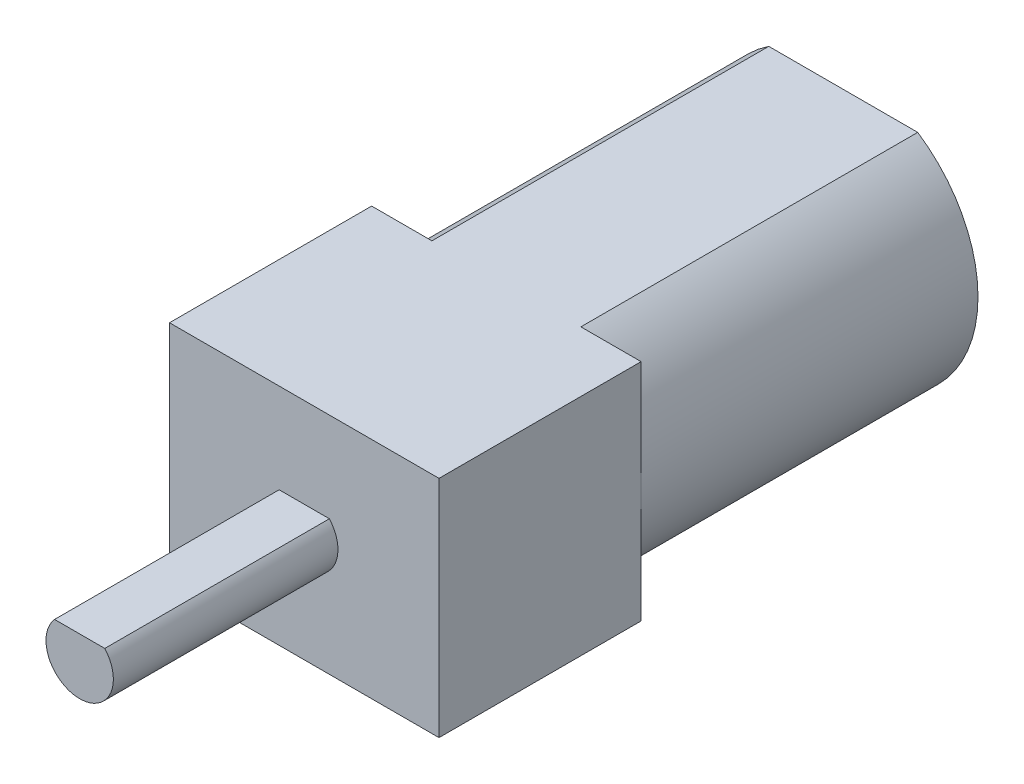
SolidWorks part; units mm, degrees
ref_plane "Front Plane" through (0, 0, 0) normal (0, 0, 1) x (1, 0, 0)
ref_plane "Top Plane" through (0, 0, 0) normal (0, 1, 0) x (1, 0, 0)
ref_plane "Right Plane" through (0, 0, 0) normal (1, 0, 0) x (0, 0, -1)
sketch "Sketch1" plane through (0, 0, 0) normal (0, 0, 1) x (1, 0, 0)
  line L0 (-3.3166, 5) -> (3.3166, 5)
  line L1 (-6, 0) -> (6, 0) construction
  line L2 (-3.3166, -5) -> (3.3166, -5)
  arc A0 (-3.3166, 5) -> (-3.3166, -5) centre (0, 0) ccw
  arc A1 (3.3166, -5) -> (3.3166, 5) centre (0, 0) ccw
  dimension "D1" = 12
  dimension "D2" = 10
extrude "Boss-Extrude1" add sketch "Sketch1" along normal blind 15
sketch "Esquisse1" plane through (0, 0, 15) normal (0, 0, 1) x (1, 0, 0)
  line L1 (6, -5) -> (-6, -5)
  line L2 (6, -5) -> (6, 5)
  line L3 (6, 5) -> (-6, 5)
  line L4 (-6, -5) -> (-6, 5)
  line L5 (6, -5) -> (-6, 5) construction
  line L6 (6, 5) -> (-6, -5) construction
  point P0 (0, 0)
  dimension "D1" = 12
  dimension "D2" = 10
extrude "Boss.-Extru.1" add sketch "Esquisse1" along normal blind 9
sketch "Esquisse2" plane through (0, 0, 0) normal (0, 0, -1) x (-1, 0, 0)
  circle A0 centre (0, 0) radius 2.5
  dimension "D1" = 5
extrude "Boss.-Extru.2" add sketch "Esquisse2" along normal blind 2
sketch "Sketch2" plane through (0, 0, 24) normal (0, 0, 1) x (1, 0, 0)
  line L0 (-1.118, 1) -> (1.118, 1)
  arc A0 (-1.118, 1) -> (1.118, 1) centre (0, 0) ccw
  dimension "D1" = 3
  dimension "D2" = 1
extrude "Boss-Extrude2" add sketch "Sketch2" along normal blind 10
